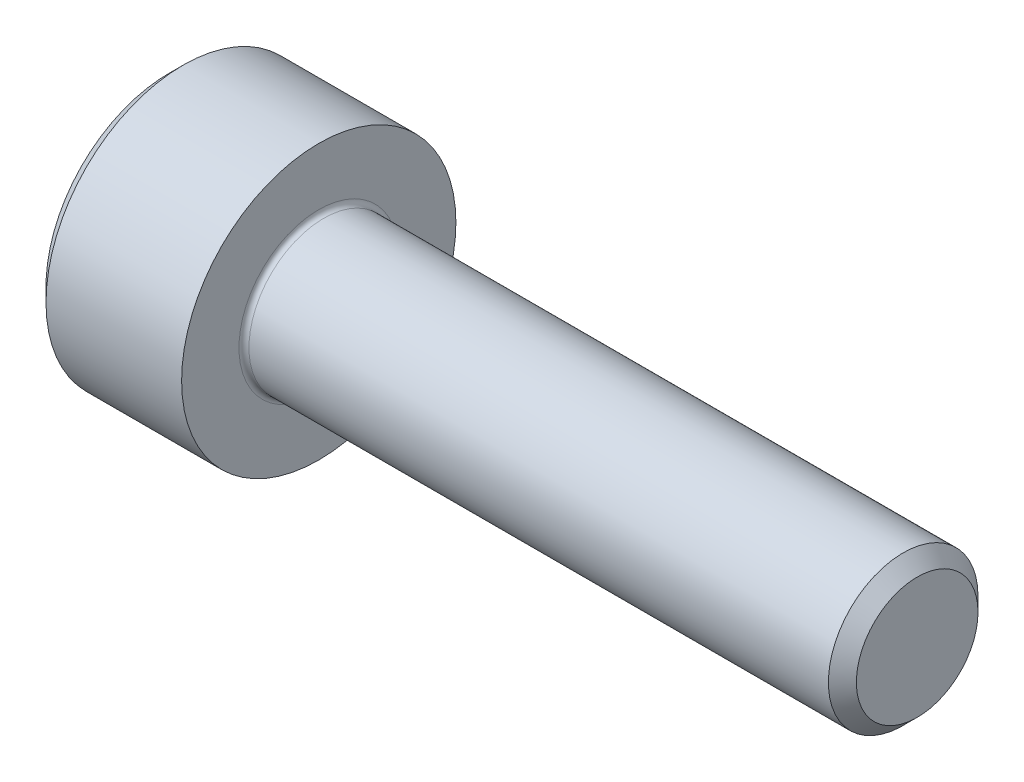
SolidWorks part; units mm, degrees
ref_plane "Front Plane" through (0, 0, 0) normal (0, 0, 1) x (1, 0, 0)
ref_plane "Top Plane" through (0, 0, 0) normal (0, 1, 0) x (1, 0, 0)
ref_plane "Right Plane" through (0, 0, 0) normal (1, 0, 0) x (0, 0, -1)
ref_plane "Plane1" through (0, 0, 0) normal (-1, 0, 0) x (0, -1, 0)
sketch "Sketch1" plane through (0, 0, 0) normal (-1, 0, 0) x (0, -1, 0)
  circle A0 centre (0, 0) radius 2.75
extrude "Boss-Extrude1" add sketch "Sketch1" against normal blind 3
sketch "Sketch2" plane through (0, 0, 0) normal (-1, 0, 0) x (0, 0, 1)
  line L0 (0, -1.478) -> (1.28, -0.739)
  line L1 (1.28, -0.739) -> (1.28, 0.739)
  line L2 (1.28, 0.739) -> (0, 1.478)
  line L3 (0, 1.478) -> (-1.28, 0.739)
  line L4 (-1.28, 0.739) -> (-1.28, -0.739)
  line L5 (-1.28, -0.739) -> (0, -1.478)
extrude "Cut-Extrude1" cut sketch "Sketch2" against normal blind 1.3
sketch "Sketch4" plane through (0, 0, 0) normal (0, 0, 1) x (1, 0, 0)
  line L0 (1.3, 1.28) -> (1.3, 0)
  line L1 (1.3, 0) -> (2.039, 0)
  line L2 (2.039, 0) -> (1.3, 1.28)
  line L3 (1.3, 0) -> (2.039, 0) construction
revolve "Cut-Revolve1" cut sketch "Sketch4" angle 360 about L1
ref_plane "Plane2" through (3, 0, 0) normal (1, 0, 0) x (0, 0, -1)
sketch "Sketch9" plane through (3, 0, 0) normal (1, 0, 0) x (0, 0, -1)
  circle A0 centre (0, 0) radius 1.5
extrude "Boss-Extrude2" add sketch "Sketch9" along normal blind 12
chamfer "Chamfer1" distance 0.2805 angle 45 2 edges at (0, 0, -2.75) (15, 0, -1.5)
fillet "Fillet1" radius 0.1 1 edges at (3, 0, -1.5)
